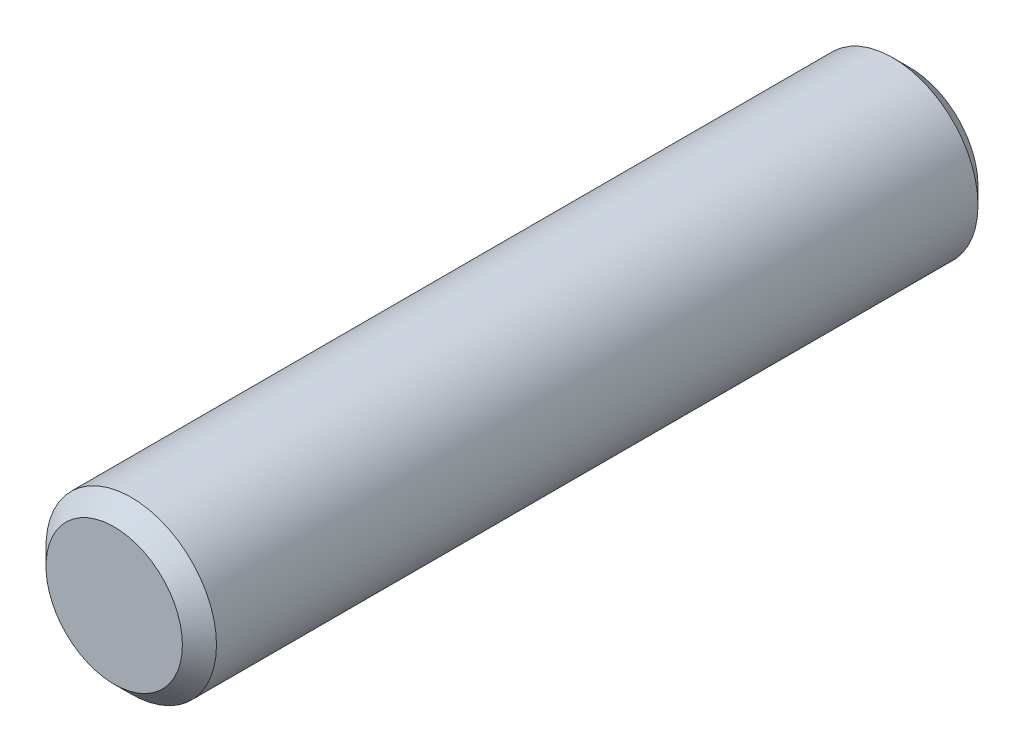
SolidWorks part; units mm, degrees
ref_plane "Front Plane" through (0, 0, 0) normal (0, 0, 1) x (1, 0, 0)
ref_plane "Top Plane" through (0, 0, 0) normal (0, 1, 0) x (1, 0, 0)
ref_plane "Right Plane" through (0, 0, 0) normal (1, 0, 0) x (0, 0, -1)
sketch "Sketch1" plane through (0, 0, 0) normal (0, 0, 1) x (1, 0, 0)
  circle A0 centre (0, 0) radius 1.5
  dimension "D1" = 3
extrude "Boss-Extrude1" add sketch "Sketch1" along normal mid plane 14
chamfer "Chamfer1" distance 0.3 angle 45 2 edges at (1.5, 0, -7) (1.5, 0, 7)
